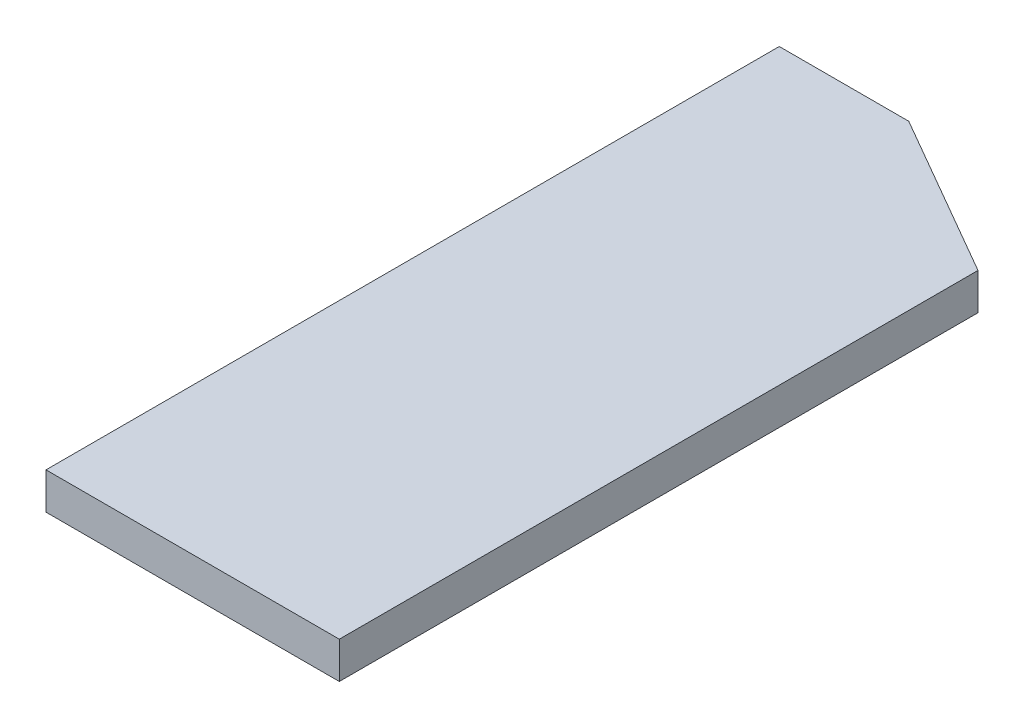
SolidWorks part; units mm, degrees
ref_plane "Спереди" through (0, 0, 0) normal (0, 0, 1) x (1, 0, 0)
ref_plane "Сверху" through (0, 0, 0) normal (0, 1, 0) x (1, 0, 0)
ref_plane "Справа" through (0, 0, 0) normal (1, 0, 0) x (0, 0, -1)
sketch "Эскиз1" plane through (0, 0, 0) normal (0, 1, 0) x (1, 0, 0)
  line L0 (0, 100) -> (17.6611, 100)
  line L1 (0, 0) -> (40, 0)
  line L2 (0, 0) -> (0, 100)
  line L4 (40, 0) -> (40, 87.1026)
  line L5 (17.6611, 100) -> (40, 87.1026)
extrude "Бобышка-Вытянуть1" add sketch "Эскиз1" along normal blind 5
